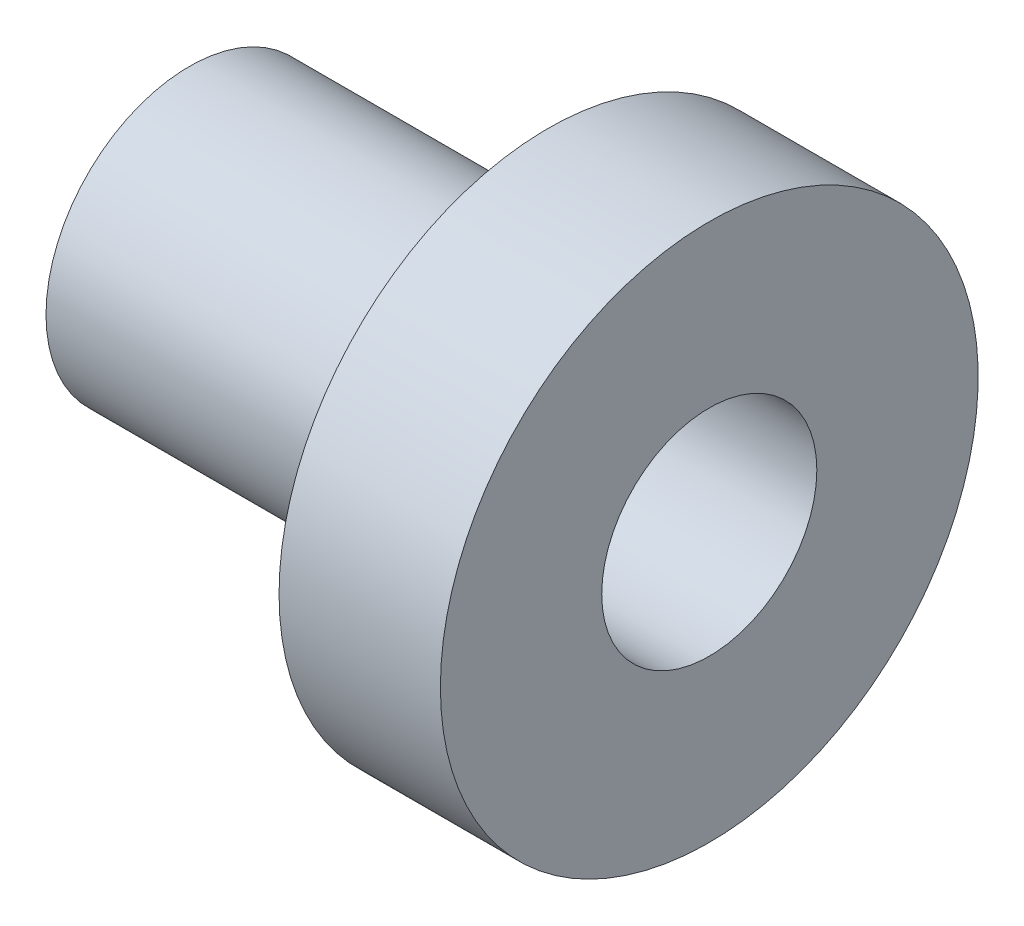
SolidWorks part; units mm, degrees
ref_plane "Plan de face" through (0, 0, 0) normal (0, 0, 1) x (1, 0, 0)
ref_plane "Plan de dessus" through (0, 0, 0) normal (0, 1, 0) x (1, 0, 0)
ref_plane "Plan de droite" through (0, 0, 0) normal (1, 0, 0) x (0, 0, -1)
sketch "Esquisse1" plane through (0, 0, 0) normal (0, 0, 1) x (1, 0, 0)
  line L0 (-32.389, 0) -> (37.2764, 0) construction
  line L1 (-9, 15) -> (0, 15)
  line L2 (0, 15) -> (0, 6)
  line L3 (0, 6) -> (-29, 6)
  line L4 (-9, 15) -> (-9, 8)
  line L5 (-9, 8) -> (-29, 8)
  line L6 (-29, 8) -> (-29, 6)
  dimension "D1" = 15
  dimension "D2" = 9
  dimension "D3" = 8
  dimension "D4" = 6
  dimension "D5" = 29
revolve "Révolution1" add sketch "Esquisse1" angle 360 about L0
